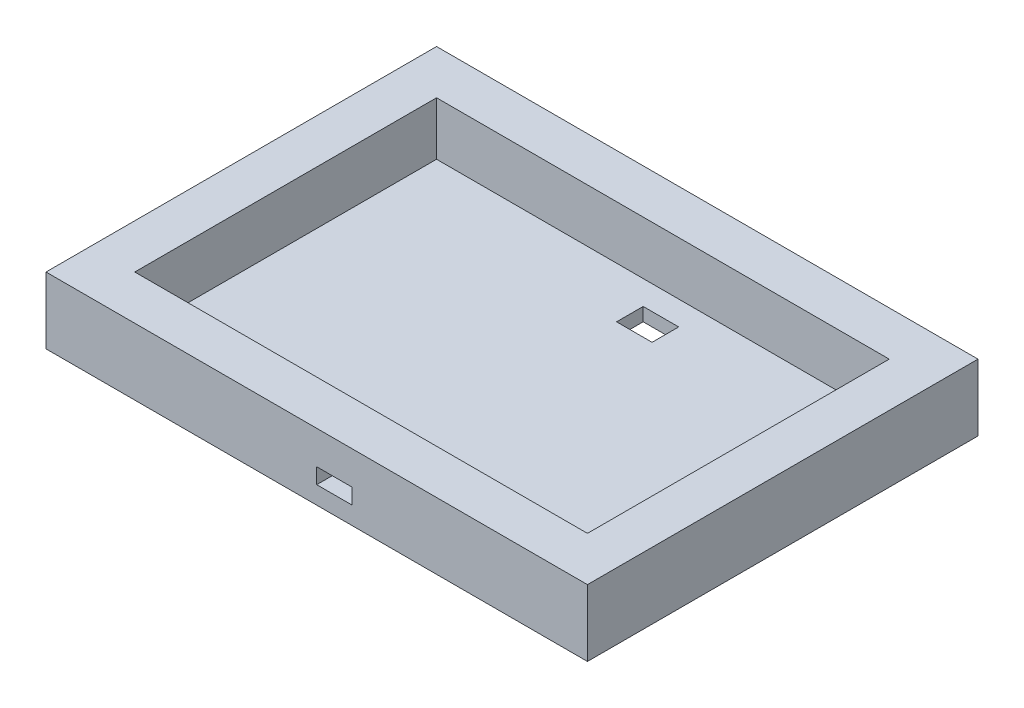
SolidWorks part; units mm, degrees
ref_plane "Front Plane" through (0, 0, 0) normal (0, 0, 1) x (1, 0, 0)
ref_plane "Top Plane" through (0, 0, 0) normal (0, 1, 0) x (1, 0, 0)
ref_plane "Right Plane" through (0, 0, 0) normal (1, 0, 0) x (0, 0, -1)
sketch "Sketch2" plane through (0, 0, 0) normal (0, 1, 0) x (1, 0, 0)
  line L1 (-92.6083, 40.4553) -> (29.3917, 40.4553)
  line L2 (-92.6083, 40.4553) -> (-92.6083, -47.5447)
  line L3 (-92.6083, -47.5447) -> (29.3917, -47.5447)
  line L4 (29.3917, 40.4553) -> (29.3917, -47.5447)
  line L9 (-82.6083, 30.4553) -> (19.3917, 30.4553)
  line L10 (-82.6083, 30.4553) -> (-82.6083, -37.5447)
  line L11 (-82.6083, -37.5447) -> (19.3917, -37.5447)
  line L12 (19.3917, 30.4553) -> (19.3917, -37.5447)
  dimension "D1" = 88
  dimension "D2" = 122
  dimension "D3" = 68
  dimension "D4" = 102
extrude "Boss-Extrude4" add sketch "Sketch2" along normal blind 15
sketch "Sketch3" plane through (0, 0, 0) normal (0, 1, 0) x (1, 0, 0)
  line L1 (-82.6083, 30.4553) -> (19.3917, 30.4553)
  line L2 (-82.6083, 30.4553) -> (-82.6083, -37.5447)
  line L3 (-82.6083, -37.5447) -> (19.3917, -37.5447)
  line L4 (19.3917, 30.4553) -> (19.3917, -37.5447)
extrude "Boss-Extrude5" add sketch "Sketch3" along normal blind 3
sketch "Sketch4" plane through (0, 0, 47.5447) normal (0, 0, 1) x (1, 0, 0)
  line L4 (-23.6083, 4) -> (-31.6083, 4)
  line L5 (-23.6083, 4) -> (-23.6083, 7.5)
  line L6 (-23.6083, 7.5) -> (-31.6083, 7.5)
  line L7 (-31.6083, 4) -> (-31.6083, 7.5)
  dimension "D3" = 8
  dimension "D4" = 3.5
extrude "Cut-Extrude1" cut sketch "Sketch4" against normal up to next and the other way through all
sketch "Sketch5" plane through (0, 3, 0) normal (0, 1, 0) x (1, 0, 0)
  line L5 (-22.6083, 25.0153) -> (-30.6083, 25.0153)
  line L6 (-22.6083, 25.0153) -> (-22.6083, 19.0153)
  line L7 (-22.6083, 19.0153) -> (-30.6083, 19.0153)
  line L8 (-30.6083, 25.0153) -> (-30.6083, 19.0153)
  dimension "D3" = 8
  dimension "D4" = 6
extrude "Cut-Extrude2" cut sketch "Sketch5" against normal through all
